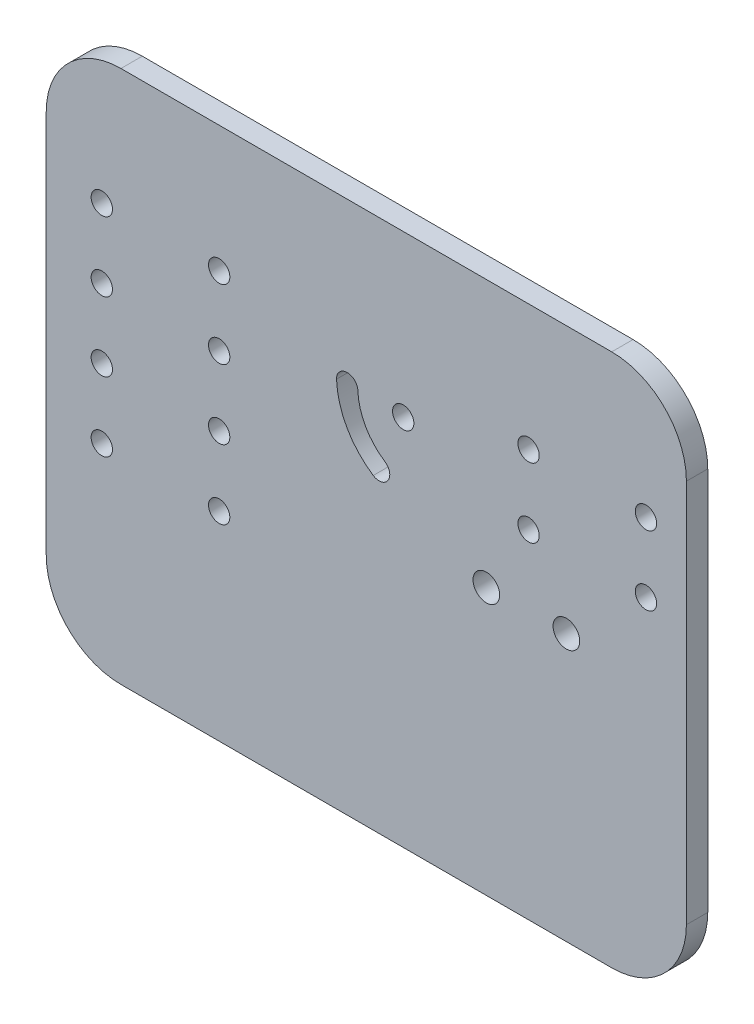
SolidWorks part; units mm, degrees
ref_plane "前视基准面" through (0, 0, 0) normal (0, 0, 1) x (1, 0, 0)
ref_plane "上视基准面" through (0, 0, 0) normal (0, 1, 0) x (1, 0, 0)
ref_plane "右视基准面" through (0, 0, 0) normal (1, 0, 0) x (0, 0, -1)
other "Configuration Table"
sketch "草图1" plane through (0, 0, 0) normal (0, 0, 1) x (1, 0, 0)
  line L1 (-52.6556, 38.8382) -> (67.3444, 38.8382)
  line L2 (-52.6556, 38.8382) -> (-52.6556, -61.1618)
  line L3 (-52.6556, -61.1618) -> (67.3444, -61.1618)
  line L4 (67.3444, 38.8382) -> (67.3444, -61.1618)
  dimension "D1" = 120
  dimension "D2" = 100
extrude "凸台-拉伸1" add sketch "草图1" along normal blind 4
fillet "圆角1" radius 14 4 edges at (67.3444, 38.8382, 2) (67.3444, -61.1618, 2) (-52.6556, -61.1618, 2) (-52.6556, 38.8382, 2)
sketch "草图2" plane through (0, 0, 4) normal (0, 0, 1) x (1, 0, 0)
  line L0 (-52.6556, 24.8382) -> (67.3444, 24.8382) construction
  line L1 (-38.6556, 38.8382) -> (-38.6556, -61.1618) construction
  line L2 (53.3444, -61.1618) -> (53.3444, 38.8382) construction
  line L3 (67.3444, -47.1618) -> (-52.6556, -47.1618) construction
  circle A0 centre (53.3444, 24.8382) radius 1.5
  circle A1 centre (-38.6556, 24.8382) radius 1.5
  circle A2 centre (-38.6556, -47.1618) radius 1.5
  circle A3 centre (53.3444, -47.1618) radius 1.5
  point P18 (53.3444, 24.8382)
  point P21 (-38.6556, 24.8382)
  point P24 (-38.6556, -47.1618)
  point P27 (53.3444, -47.1618)
  dimension "D1" = 3
extrude "切除-拉伸1" [suppressed] cut sketch "草图2" against normal through all
sketch "草图7" plane through (0, 0, 0) normal (0, 0, -1) x (-1, 0, 0)
  line L0 (-67.3444, -11.1618) -> (52.6556, -11.1618) construction
  line L1 (-67.3444, -47.1618) -> (-67.3444, 24.8382) construction
  line L2 (52.6556, 24.8382) -> (52.6556, -47.1618) construction
  circle A0 centre (-44.8444, -11.1618) radius 2.5
  circle A1 centre (-29.8444, -11.1618) radius 2.5
  dimension "D2" = 5
  dimension "D4" = 5
  dimension "D1" = 22.5
  dimension "D3" = 15
extrude "切除-拉伸2" cut sketch "草图7" against normal through all
sketch "草图14" plane through (0, 0, 0) normal (0, 0, -1) x (-1, 0, 0)
  arc A17 (-1.7605, 8.6095) -> (-5.7577, 8.7588) centre (-3.7591, 8.6842) ccw
  arc A18 (-10.8349, -0.2381) -> (-8.6409, -3.5827) centre (-9.7379, -1.9104) ccw
  arc A19 (-8.6409, -3.5827) -> (-1.7605, 8.6095) centre (-17.0126, 9.1793) ccw
  circle A20 centre (42.2409, -23.8158) radius 2
  circle A21 centre (20.2409, -23.8158) radius 2
  circle A22 centre (42.2409, -10.8158) radius 2
  circle A23 centre (20.2409, -10.8158) radius 2
  circle A24 centre (42.2409, 2.1842) radius 2
  circle A25 centre (42.2409, 15.1842) radius 2
  circle A26 centre (20.2409, 2.1842) radius 2
  circle A27 centre (20.2409, 15.1842) radius 2
  arc A28 (-10.8349, -0.2381) -> (-5.7577, 8.7588) centre (-17.0126, 9.1793) ccw
  circle A29 centre (-14.2591, 8.6842) radius 2
  circle A30 centre (-37.7591, 2.1842) radius 2
  circle A31 centre (-59.7591, 2.1842) radius 2
  circle A32 centre (-59.7591, 15.1842) radius 2
  circle A33 centre (-37.7591, 15.1842) radius 2
  point P10 (0, 0)
extrude "切除-拉伸3" cut sketch "草图14" against normal through all
